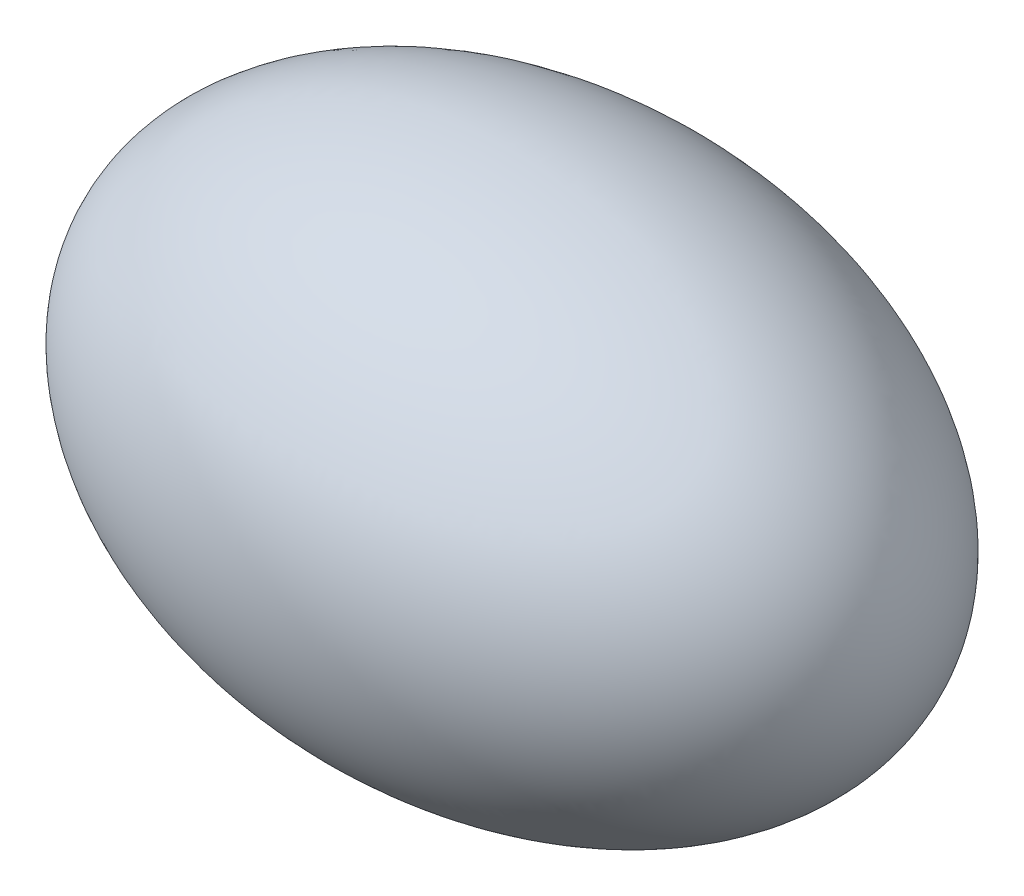
SolidWorks part; units mm, degrees
ref_plane "Спереди" through (0, 0, 0) normal (0, 0, 1) x (1, 0, 0)
ref_plane "Сверху" through (0, 0, 0) normal (0, 1, 0) x (1, 0, 0)
ref_plane "Справа" through (0, 0, 0) normal (1, 0, 0) x (0, 0, -1)
other "Configuration Table"
sketch "Эскиз5" plane through (0, 0, 0) normal (0, 1, 0) x (1, 0, 0)
  line L0 (-814.6818, -7.9877) -> (685.3182, -7.9877) construction
  line L1 (-814.6818, -7.9877) -> (685.3182, -7.9877)
  ellipse E0 centre (-64.6818, -7.9877) end of major axis (685.3182, -7.9877) minor radius 500 (685.3182, -7.9877) -> (-814.6818, -7.9877) ccw
  dimension "D1" = 1500
  dimension "D2" = 1000
revolve "Повернуть1" add sketch "Эскиз5" angle 360 about L0
equation "\"10нм.\"=10"
